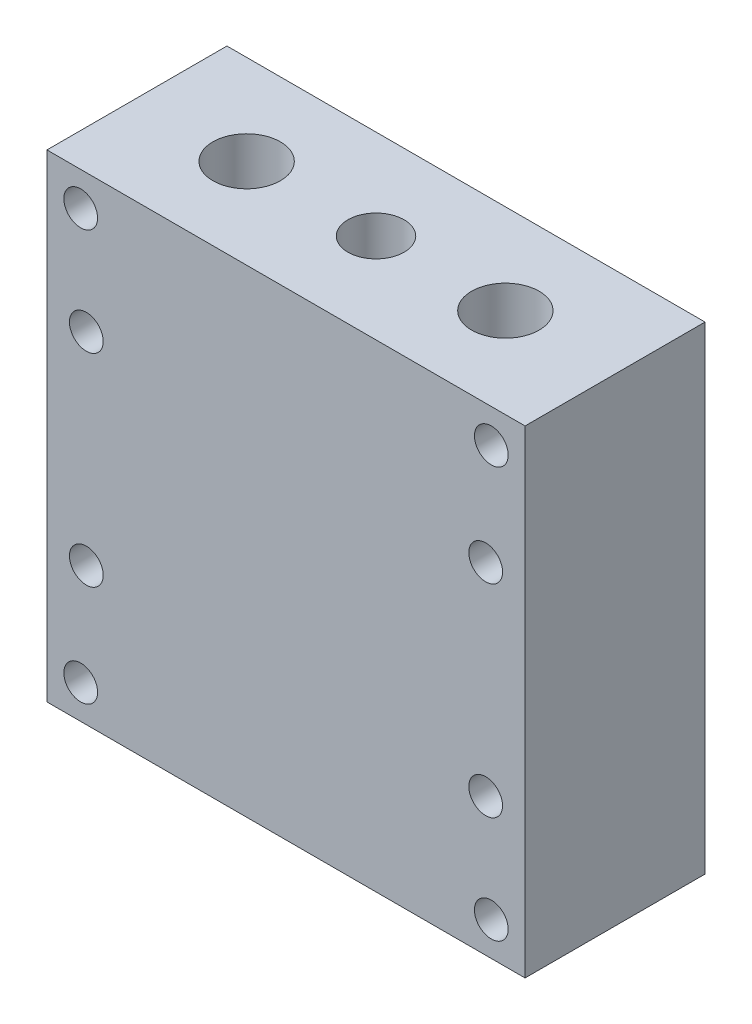
SolidWorks part; units mm, degrees
ref_plane "Front Plane" through (0, 0, 0) normal (0, 0, 1) x (1, 0, 0)
ref_plane "Top Plane" through (0, 0, 0) normal (0, 1, 0) x (1, 0, 0)
ref_plane "Right Plane" through (0, 0, 0) normal (1, 0, 0) x (0, 0, -1)
sketch "Sketch1" plane through (0, 0, 0) normal (0, 0, 1) x (1, 0, 0)
  line L1 (-42.5, -42.5) -> (42.5, -42.5)
  line L2 (-42.5, -42.5) -> (-42.5, 42.5)
  line L3 (-42.5, 42.5) -> (42.5, 42.5)
  line L4 (42.5, -42.5) -> (42.5, 42.5)
  line L5 (-42.5, -42.5) -> (42.5, 42.5) construction
  line L6 (-42.5, 42.5) -> (42.5, -42.5) construction
  point P0 (0, 0)
  dimension "D1" = 85
  dimension "D2" = 85
extrude "Boss-Extrude1" add sketch "Sketch1" along normal blind 32
sketch "Sketch2" plane through (0, 0, 32) normal (0, 0, 1) x (1, 0, 0)
  line L0 (0, 59.3297) -> (0, -60.1757) construction
  line L1 (-66.8015, 0) -> (43.3972, 0) construction
  circle A0 centre (-36.5, 36.5) radius 3
  circle A1 centre (36.5, 36.5) radius 3
  circle A2 centre (36.5, -36.5) radius 3
  circle A3 centre (-36.5, -36.5) radius 3
  dimension "D1" = 6
  dimension "D2" = 36.5
  dimension "D3" = 36.5
extrude "Cut-Extrude1" cut sketch "Sketch2" against normal through all
sketch "Sketch3" plane through (0, 42.5, 0) normal (0, 1, 0) x (1, 0, 0)
  line L0 (-53.9134, -16) -> (57.8859, -16) construction
  line L1 (42.5, 0) -> (-42.5, 0) construction
  line L2 (0, 13.8415) -> (0, -43.9498) construction
  line L3 (42.5, -32) -> (-42.5, -32) construction
  circle A0 centre (0, -16) radius 5
  circle A1 centre (-23, -16) radius 6
  circle A2 centre (23, -16) radius 6
  dimension "D2" = 12
  dimension "D3" = 10
  dimension "D1" = 16
  dimension "D4" = 23
  dimension "D5" = 16
extrude "Cut-Extrude2" cut sketch "Sketch3" against normal through all
sketch "Sketch4" plane through (0, 0, 0) normal (0, 0, -1) x (-1, 0, 0)
  line L0 (-55.2042, 0) -> (67.567, 0) construction
  line L1 (0, 45.8403) -> (0, -47.9211) construction
  circle A0 centre (-35.5, 18) radius 3
  circle A1 centre (-35.5, -18) radius 3
  circle A2 centre (35.5, -18) radius 3
  circle A3 centre (35.5, 18) radius 3
  dimension "D1" = 6
  dimension "D2" = 35.5
  dimension "D3" = 18
extrude "Cut-Extrude3" cut sketch "Sketch4" against normal through all
